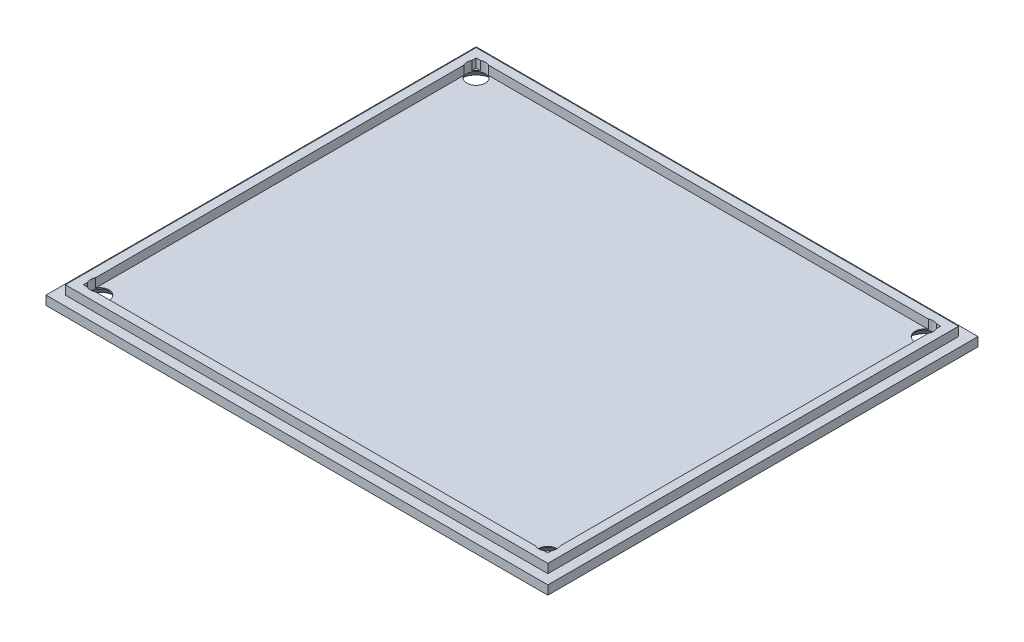
SolidWorks part; units mm, degrees
material "6061-T6 (SS)"
ref_plane "Front Plane" through (0, 0, 0) normal (0, 0, 1) x (1, 0, 0)
ref_plane "Top Plane" through (0, 0, 0) normal (0, 1, 0) x (1, 0, 0)
ref_plane "Right Plane" through (0, 0, 0) normal (1, 0, 0) x (0, 0, -1)
sketch "Sketch1" plane through (0, 0, 0) normal (0, 1, 0) x (1, 0, 0)
  line L1 (-44.45, 38.1) -> (44.45, 38.1)
  line L2 (-44.45, 38.1) -> (-44.45, -38.1)
  line L3 (-44.45, -38.1) -> (44.45, -38.1)
  line L4 (44.45, 38.1) -> (44.45, -38.1)
  line L5 (-44.45, 38.1) -> (44.45, -38.1) construction
  line L6 (-44.45, -38.1) -> (44.45, 38.1) construction
  point P0 (0, 0)
  dimension "D1" = 88.9
  dimension "D2" = 76.2
extrude "Boss-Extrude1" add sketch "Sketch1" along normal blind 1.5875
sketch "Sketch2" plane through (0, 1.5875, 0) normal (0, 1, 0) x (1, 0, 0)
  line L0 (44.45, -38.1) -> (44.45, 38.1) construction
  line L1 (-44.45, -38.1) -> (44.45, -38.1) construction
  line L2 (-44.45, 38.1) -> (-44.45, -38.1) construction
  line L3 (44.45, 38.1) -> (-44.45, 38.1) construction
  line L4 (44.45, -38.1) -> (44.45, 38.1) construction
  line L5 (-44.45, -38.1) -> (44.45, -38.1) construction
  line L6 (-44.45, 38.1) -> (-44.45, -38.1) construction
  line L7 (44.45, 38.1) -> (-44.45, 38.1) construction
  line L8 (42.7355, -36.3855) -> (42.7355, 36.3855)
  line L9 (42.7355, 36.3855) -> (-42.7355, 36.3855)
  line L10 (-42.7355, 36.3855) -> (-42.7355, -36.3855)
  line L11 (-42.7355, -36.3855) -> (42.7355, -36.3855)
  line L12 (41.148, -34.798) -> (41.148, 34.798)
  line L13 (41.148, 34.798) -> (-41.148, 34.798)
  line L14 (-41.148, 34.798) -> (-41.148, -34.798)
  line L15 (-41.148, -34.798) -> (41.148, -34.798)
  dimension "D1" = 1.7145
  dimension "D2" = 1.5875
extrude "Boss-Extrude2" add sketch "Sketch2" along normal blind 1.5875
hole_wizard "CSK for #4 Flat Head Machine Screw1" positions "Sketch3" profile "Sketch4" countersink size "#4" standard "ANSI Inch"
sketch "Sketch3" plane through (28.4819, 0, -59.3955) normal (0, -1, 0) x (-1, 0, 0)
  point P0 (-11.2056, -26.058)
  point P3 (68.1694, -26.058)
  point P6 (68.1694, -92.733)
  point P9 (-11.2056, -92.733)
sketch "Sketch4" plane through (39.6875, 0, -33.3375) normal (1, 0, 0) x (0, 0, -1)
  line L0 (0, 0) -> (0, 4.1546)
  line L1 (0, 4.1546) -> (1.6319, 3.174)
  line L2 (1.6319, 3.174) -> (1.6319, 1.4098)
  line L3 (1.6319, 1.4098) -> (2.8575, 0)
  line L4 (2.8575, 0) -> (0, 0)
  line L5 (-1.632, 1.4098) -> (-2.8575, 0) construction
  line L6 (0, 4.1546) -> (-1.632, 3.174) construction
  line L7 (0, -6.35) -> (0, 107.95) construction
  dimension "Hole Dia." = 3.2639
  dimension "Hole Depth" = 3.174
  dimension "Near C'Sink Dia." = 5.715
  dimension "Near C'Sink Angle" = 82
  dimension "Drill Angle" = 118
